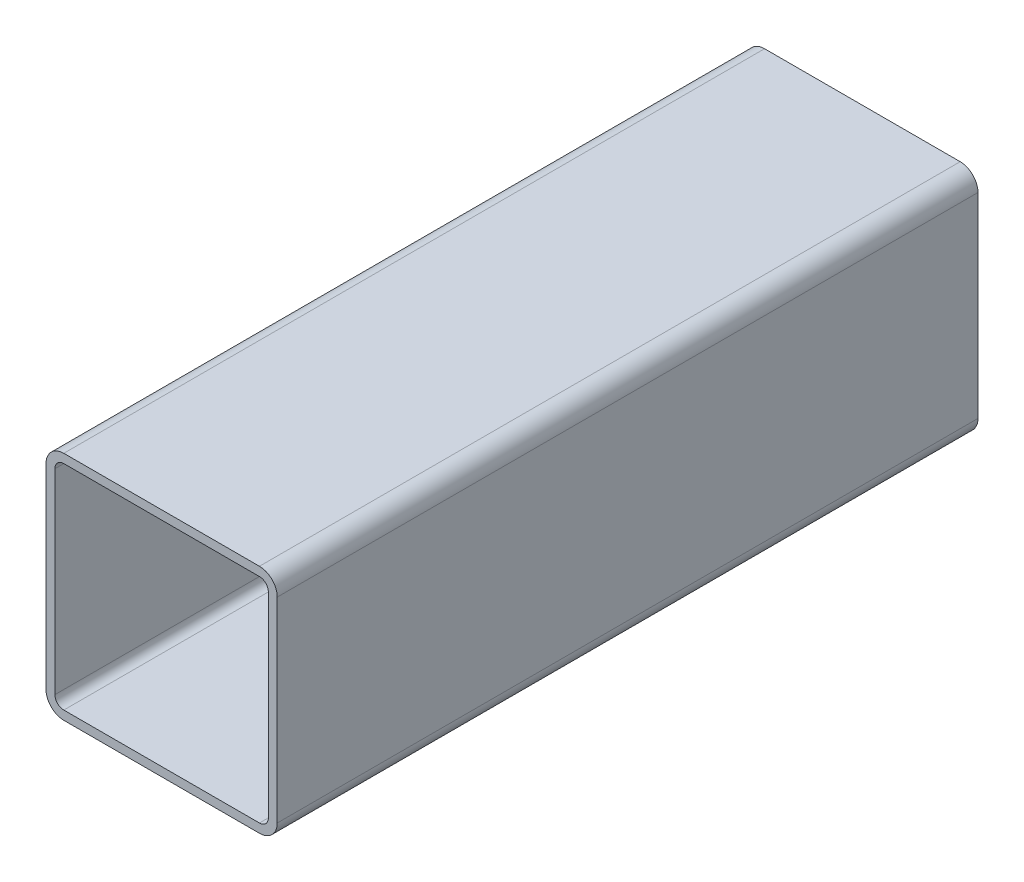
SolidWorks part; units mm, degrees
ref_plane "Front Plane" through (0, 0, 0) normal (0, 0, 1) x (1, 0, 0)
ref_plane "Top Plane" through (0, 0, 0) normal (0, 1, 0) x (1, 0, 0)
ref_plane "Right Plane" through (0, 0, 0) normal (1, 0, 0) x (0, 0, -1)
sketch "Sketch1" plane through (0, 0, 0) normal (0, 0, 1) x (1, 0, 0)
  line L1 (-2.792, -3.3) -> (2.792, -3.3)
  line L2 (-3.3, -2.792) -> (-3.3, 2.792)
  line L3 (-2.792, 3.3) -> (2.792, 3.3)
  line L4 (3.3, -2.792) -> (3.3, 2.792)
  line L5 (-3.3, -3.3) -> (3.3, 3.3) construction
  line L6 (-3.3, 3.3) -> (3.3, -3.3) construction
  arc A0 (-3.3, 2.792) -> (-2.792, 3.3) centre (-2.792, 2.792) cw
  arc A1 (-2.792, -3.3) -> (-3.3, -2.792) centre (-2.792, -2.792) cw
  arc A2 (2.792, -3.3) -> (3.3, -2.792) centre (2.792, -2.792) ccw
  arc A3 (2.792, 3.3) -> (3.3, 2.792) centre (2.792, 2.792) cw
  point P0 (0, 0)
  dimension "D2" = 0.508
  dimension "D1" = 6.6
extrude "Extrude-Thin1" add sketch "Sketch1" along normal mid plane 20 thin thin type one direction reverse wall 0.254
